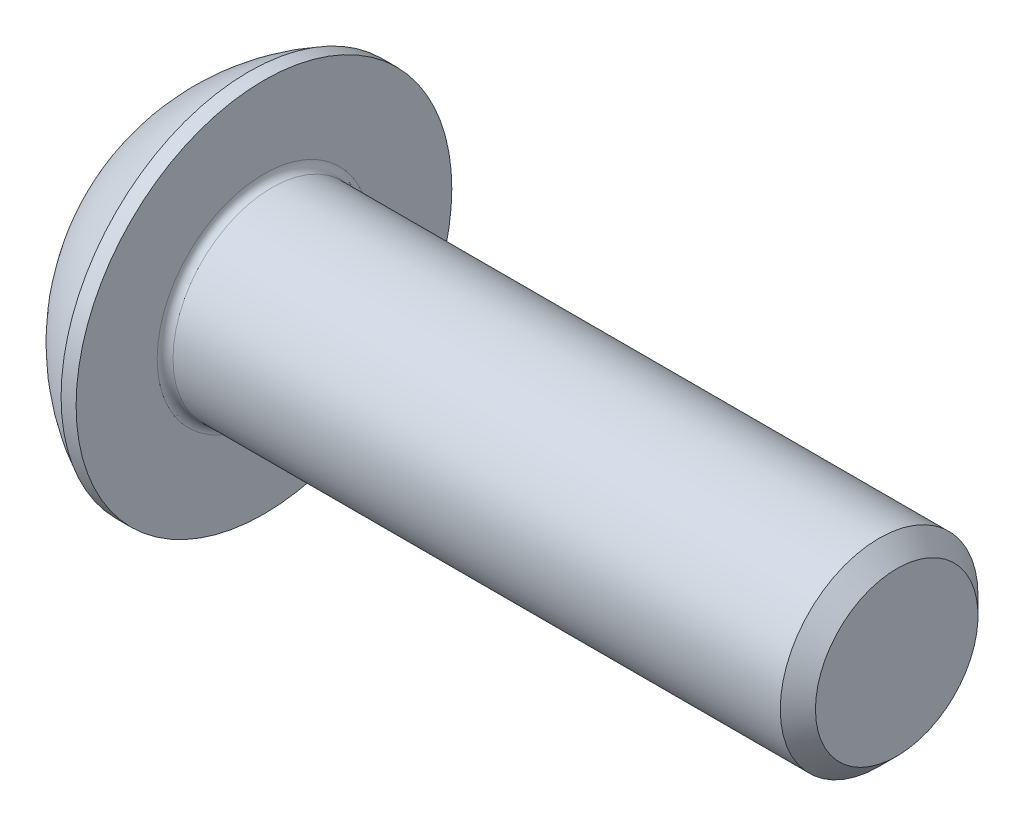
SolidWorks part; units mm, degrees
ref_plane "Plane1" through (0, 0, 0) normal (0, 0, 1) x (1, 0, 0)
ref_plane "Plane2" through (0, 0, 0) normal (0, 1, 0) x (1, 0, 0)
ref_plane "Plane3" through (0, 0, 0) normal (1, 0, 0) x (0, 0, -1)
sketch "BodySke" plane through (0, 0, 0) normal (0, 0, 1) x (1, 0, 0)
  line L0 (18.75, 0) -> (18.75, 2.055)
  line L1 (18.305, 2.5) -> (2.75, 2.5)
  line L2 (2.75, 2.5) -> (2.75, 4.75)
  line L3 (2.75, 4.75) -> (2.37, 4.75)
  line L4 (0, 0) -> (101.6, 0) construction
  line L5 (2.75, -4.75) -> (2.37, -4.75) construction
  line L6 (55.6768, -2.5) -> (2.75, -2.5) construction
  line L7 (18.75, 0) -> (0, 0)
  line L8 (0, 2.375) -> (0, -2.375) construction
  line L9 (0, 0) -> (0, 2.375)
  line L10 (18.75, 2.055) -> (18.305, 2.5)
  line L11 (18.75, -2.055) -> (18.305, -2.5) construction
  line L12 (3.55, 9.525) -> (3.55, -2.5) construction
  line L13 (6.75, 9.525) -> (6.75, -2.5) construction
  arc A1 (0, 2.375) -> (2.37, 4.75) centre (4.755, 0) cw
  dimension "Diameter" = 5
  dimension "Length" = 16
  dimension "Head_dia" = 9.5
  dimension "D1" = 4.75
  dimension "Head_ht" = 2.75
  dimension "Head_side_ht" = 0.38
  dimension "Minor_dia" = 4.11
  dimension "Body_ch_ang" = 45
  dimension "Advance" = 0.8
revolve "BaseBody" add sketch "BodySke" angle 360 about L4
cosmetic thread "ThreadCosmetic" [suppressed] parameters "Thread_length"=12, "Thread_minor"=4.11
fillet "Fillet1" radius 0.2 1 edges at (2.75, 0, 2.5)
sketch "Sketch2" plane through (0, 0, 0) normal (0, 0, 1) x (1, 0, 0)
  line L0 (0, 1.5) -> (1.56, 1.5)
  line L1 (1.56, 1.5) -> (2.426, 0)
  line L3 (2.426, 0) -> (0, 0)
  line L4 (0, 0) -> (0, 1.5)
  line L5 (0, -1.5) -> (1.56, -1.5) construction
  line L6 (0, 0) -> (47.625, 0) construction
  dimension "D2" = 60
  dimension "PreBroach_depth" = 1.56
  dimension "PreBroach_dia" = 3
revolve "PreBroach" cut sketch "Sketch2" angle 360 about L6
sketch "Sketch3" plane through (0, 0, 0) normal (1, 0, 0) x (0, 0, -1)
  line L0 (-1.5, -0.866) -> (-1.5, 0.866)
  line L1 (-1.5, 0.866) -> (0, 1.7321)
  line L2 (0, 1.7321) -> (1.5, 0.866)
  line L3 (1.5, 0.866) -> (1.5, -0.866)
  line L4 (1.5, -0.866) -> (0, -1.7321)
  line L5 (0, -1.7321) -> (-1.5, -0.866)
  dimension "Hex_size" = 3
  dimension "D3" = 3
  dimension "D1" = 1.5
  dimension "D2" = 1.5
extrude "Hex" cut sketch "Sketch3" along normal blind 1.56
sketch "ThdSchSke" plane through (0, 0, 0) normal (0, 0, 1) x (1, 0, 0)
  line L0 (6.75, -2.055) -> (6.4384, -2.5)
  line L1 (6.75, -2.055) -> (7.0616, -2.5)
  line L2 (7.0616, -2.5) -> (7.0616, -3.125)
  line L3 (-3.175, 0) -> (5.1513, 0) construction
  line L5 (7.0616, -3.125) -> (6.4384, -3.125)
  line L6 (6.4384, -3.125) -> (6.4384, -2.5)
  dimension "Diameter" = 5
  dimension "Thread_minor" = 4.11
  dimension "SideAngle" = 55
  dimension "VeeAngle" = 70
  dimension "Overcut" = 6.25
revolve "ThreadSchematic" [suppressed] cut sketch "ThdSchSke" angle 360 about L3
pattern_linear "ThdSchPat" [suppressed]
equation "\"D1@BodySke\" = \"Head_dia@BodySke\" * .5"
equation "\"Thread_minor@ThreadCosmetic\" = \"Minor_dia@BodySke\""
equation "\"D1@Sketch3\" = \"Hex_size@Sketch3\" / 2"
equation "\"D2@Sketch3\" = \"D1@Sketch3\""
equation "\"D3@Sketch3\" = \"Hex_size@Sketch3\""
equation "\"Thread_length@ThreadCosmetic\" = ((sgn( (\"Length@BodySke\" - \"Advance@BodySke\" * 2.0) - \"Thread_nom@BodySke\" )-1)*( (\"Length@BodySke\" - \"Advance@BodySke\" * 2.0) - \"Thread_nom@BodySke\" ))/-2+ \"Thread_nom@BodySke\""
equation "\"Thread_minor@ThdSchSke\" = \"Minor_dia@BodySke\""
equation "\"Diameter@ThdSchSke\" = \"Diameter@BodySke\""
equation "\"Overcut@ThdSchSke\" = \"Diameter@BodySke\" * 1.25"
equation "\"Start@ThdSchSke\" = \"Head_ht@BodySke\" + \"Length@BodySke\" - \"Thread_length@ThreadCosmetic\"  '---Non-countersunk---"
equation "\"Num_threads@ThdSchPat\" = int( \"Thread_length@ThreadCosmetic\" / \"Advance@BodySke\" + 0.999 )  + 1"
equation "\"Advance@ThdSchPat\" = \"Thread_length@ThreadCosmetic\" /  (\"Num_threads@ThdSchPat\" - 1) 'relax it"
equation "\"Num_threads@ThdSchPat\" = \"Num_threads@ThdSchPat\" - sgn( \"Num_threads@ThdSchPat\" - 1) '---chamfered tips only---"
